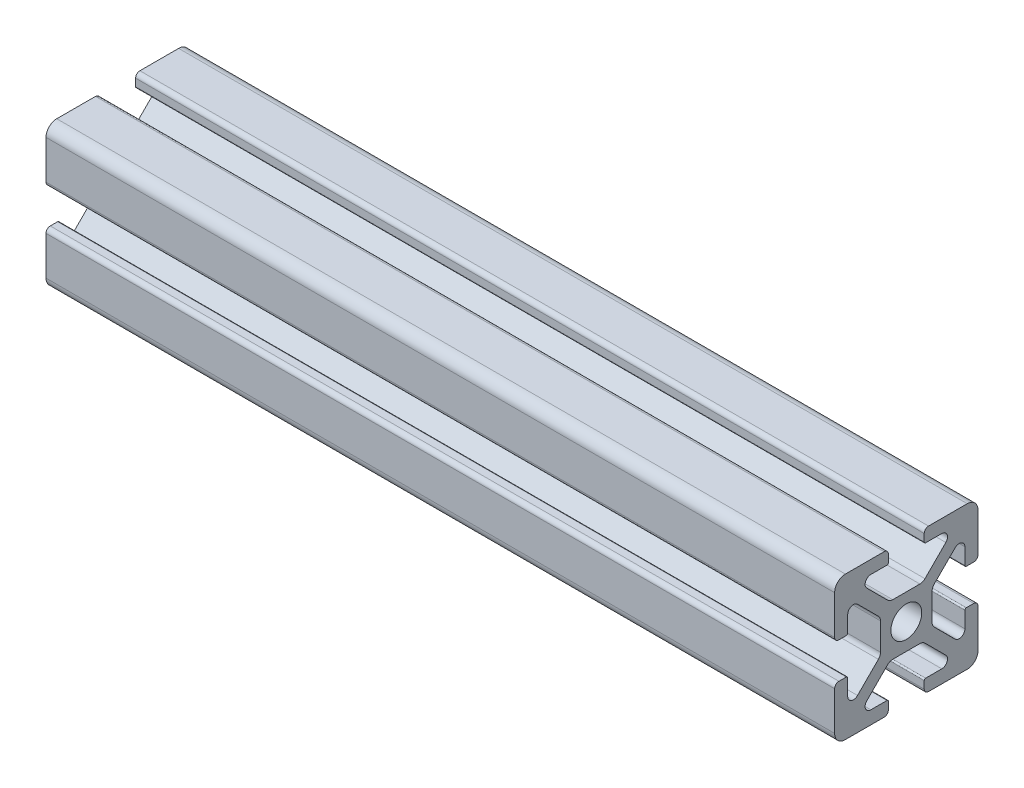
SolidWorks part; units mm, degrees
ref_plane "Front Plane" through (0, 0, 0) normal (0, 0, 1) x (1, 0, 0)
ref_plane "Top Plane" through (0, 0, 0) normal (0, 1, 0) x (1, 0, 0)
ref_plane "Right Plane" through (0, 0, 0) normal (1, 0, 0) x (0, 0, -1)
sketch "Sketch1" plane through (0, 0, 0) normal (1, 0, 0) x (0, 0, -1)
  line L0 (0, -10) -> (0, 10) construction
  line L1 (10, -10) -> (-10, -10)
  line L2 (10, -10) -> (10, 10)
  line L3 (10, 10) -> (0, 10)
  line L4 (-10, -10) -> (-10, 10)
  line L5 (10, -10) -> (-10, 10) construction
  line L6 (10, 10) -> (-10, -10) construction
  line L7 (10, 0) -> (-10, 0) construction
  line L8 (-2.5, 9.4) -> (-2.5, 8.3731)
  line L9 (-2.7, 8.1731) -> (-4.95, 8.1731)
  line L10 (-5.5157, 6.8075) -> (-2.6011, 3.8929)
  line L11 (-1.894, 3.6) -> (0, 3.6)
  line L12 (-5.3502, 4.0584) -> (-4.0584, 5.3502) construction
  line L13 (-3.825, 8.1731) -> (-3.825, 10) construction
  line L14 (-3.1, 10) -> (-10, 10)
  line L15 (-5.75, 7.3731) -> (5.75, 7.3731) construction
  circle A0 centre (0, 0) radius 2.15
  arc A1 (-4.95, 8.1731) -> (-5.5157, 6.8075) centre (-4.95, 7.3731) ccw
  arc A2 (-2.6011, 3.8929) -> (-1.894, 3.6) centre (-1.894, 4.6) ccw
  arc A3 (-2.5, 8.3731) -> (-2.7, 8.1731) centre (-2.7, 8.3731) cw
  arc A4 (-2.5, 9.4) -> (-3.1, 10) centre (-3.1, 9.4) ccw
  point P0 (0, 0)
  point P9 (0, 0)
  point P12 (0, 0)
  point P22 (-4.7043, 4.7043)
  point P32 (-2.5, 10)
  point P33 (-2.5, 8.8866)
  point P35 (-4.0584, 5.3502)
  point P37 (0, 7.3731)
  dimension "Center Hole Diameter" = 4.3
  dimension "D4" = 1
  dimension "D5" = 0.2
  dimension "D6" = 0.6
  dimension "D3" = 0.8
  dimension "Rail Height" = 20
  dimension "D7" = 6.4
  dimension "T Slot Width" = 5
  dimension "D10" = 10
  dimension "Rail Width" = 20
  dimension "D2" = 11.5
sketch "Sketch2" plane through (0, 0, 0) normal (0, 0, 1) x (1, 0, 0)
  line L0 (-132.4, 10) -> (-132.4, -10) construction
  line L1 (152.4, -10) -> (-152.4, -10) construction
  line L2 (152.4, -10) -> (152.4, 10) construction
  line L3 (152.4, 10) -> (-152.4, 10) construction
  line L4 (-152.4, -10) -> (-152.4, 10) construction
  line L5 (152.4, -10) -> (-152.4, 10) construction
  line L6 (152.4, 10) -> (-152.4, -10) construction
  line L7 (132.4, 10) -> (132.4, -10) construction
  point P0 (0, 0)
  point P12 (132.4, 0)
  dimension "Length" = 304.8
  dimension "D1" = 20
  dimension "D2" = 20
sketch "Sketch3" plane through (0, 0, 0) normal (1, 0, 0) x (0, 0, -1)
  line L0 (-5.5157, 6.8075) -> (-2.6011, 3.8929) construction
  line L5 (-3.1, 10) -> (-10, 10) construction
  line L6 (-2.5, 9.4) -> (-2.5, 8.3731) construction
  line L7 (-2.7, 8.1731) -> (-4.95, 8.1731) construction
  line L8 (-1.894, 3.6) -> (0, 3.6) construction
  line L9 (-5.5157, 6.8075) -> (-2.6011, 3.8929)
  line L10 (-10, 10) -> (0, 0) construction
  line L12 (-3.6, 1.894) -> (-3.6, 0)
  line L13 (-8.1731, 2.7) -> (-8.1731, 4.95)
  line L14 (-3.1, 10) -> (-8.5, 10)
  line L15 (-2.5, 9.4) -> (-2.5, 8.3731)
  line L16 (-2.7, 8.1731) -> (-4.95, 8.1731)
  line L17 (-1.894, 3.6) -> (0, 3.6)
  line L18 (-9.4, 2.5) -> (-8.3731, 2.5)
  line L19 (-10, 3.1) -> (-10, 8.5)
  line L20 (-6.8075, 5.5157) -> (-3.8929, 2.6011)
  line L21 (-3.6, 0) -> (-2.15, 0)
  line L22 (0, 3.6) -> (0, 2.15)
  arc A0 (-2.5, 9.4) -> (-3.1, 10) centre (-3.1, 9.4) ccw construction
  arc A1 (-2.7, 8.1731) -> (-2.5, 8.3731) centre (-2.7, 8.3731) ccw construction
  arc A2 (-4.95, 8.1731) -> (-5.5157, 6.8075) centre (-4.95, 7.3731) ccw construction
  arc A3 (-2.6011, 3.8929) -> (-1.894, 3.6) centre (-1.894, 4.6) ccw construction
  arc A4 (-2.5, 9.4) -> (-3.1, 10) centre (-3.1, 9.4) ccw
  arc A5 (-2.7, 8.1731) -> (-2.5, 8.3731) centre (-2.7, 8.3731) ccw
  arc A6 (-4.95, 8.1731) -> (-5.5157, 6.8075) centre (-4.95, 7.3731) ccw
  arc A7 (-2.6011, 3.8929) -> (-1.894, 3.6) centre (-1.894, 4.6) ccw
  arc A8 (-3.8929, 2.6011) -> (-3.6, 1.894) centre (-4.6, 1.894) cw
  arc A9 (-8.1731, 4.95) -> (-6.8075, 5.5157) centre (-7.3731, 4.95) cw
  arc A10 (-8.1731, 2.7) -> (-8.3731, 2.5) centre (-8.3731, 2.7) cw
  arc A11 (-9.4, 2.5) -> (-10, 3.1) centre (-9.4, 3.1) cw
  circle A12 centre (0, 0) radius 2.15 construction
  arc A13 (0, 2.15) -> (-2.15, 0) centre (0, 0) ccw
  arc A14 (-10, 8.5) -> (-8.5, 10) centre (-8.5, 8.5) cw
  dimension "D1" = 1.5
extrude "Boss-Extrude1" add sketch "Sketch3" against normal blind 110
mirror "Mirror1" about plane through (0, 0, 0) normal (0, 1, 0) of bodies 104
mirror "Mirror2" about plane through (0, 0, 0) normal (0, 0, 1) of bodies 105
equation "\"D10@Sketch1\" = \"Rail Height@Sketch1\" / 2"
equation "\"D2@Sketch2\"=\"D1@Sketch2\""
